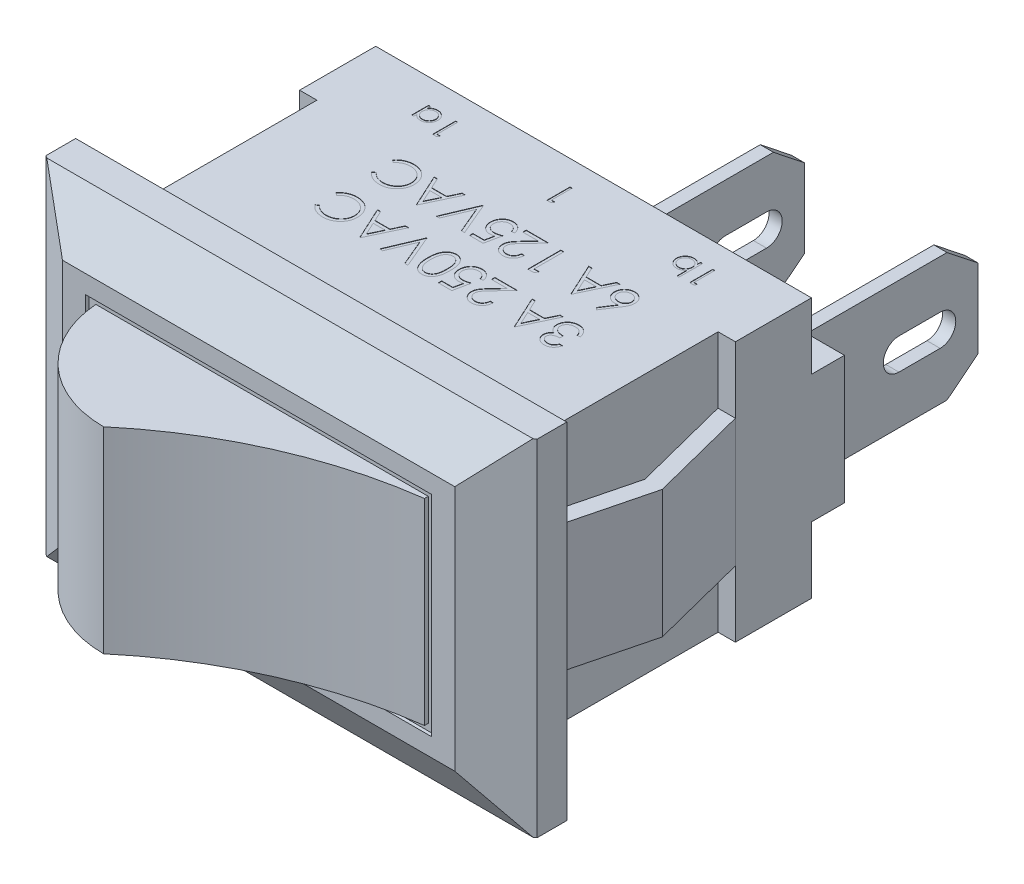
SolidWorks part; units mm, degrees
ref_plane "Front Plane" through (0, 0, 0) normal (0, 0, 1) x (1, 0, 0)
ref_plane "Top Plane" through (0, 0, 0) normal (0, 1, 0) x (1, 0, 0)
ref_plane "Right Plane" through (0, 0, 0) normal (1, 0, 0) x (0, 0, -1)
sketch "Sketch1" plane through (0, 0, 0) normal (0, 0, 1) x (1, 0, 0)
  line L1 (-7.455, 5.24) -> (7.455, 5.24)
  line L2 (-7.455, 5.24) -> (-7.455, -5.24)
  line L3 (-7.455, -5.24) -> (7.455, -5.24)
  line L4 (7.455, 5.24) -> (7.455, -5.24)
  dimension "D1" = 14.91
  dimension "D2" = 7.455
  dimension "D3" = 10.48
  dimension "D4" = 5.24
extrude "Boss-Extrude1" add sketch "Sketch1" against normal blind 1.9
sketch "Sketch2" plane through (0, -5.24, 0) normal (0, -1, 0) x (1, 0, 0)
  line L0 (-7.455, -1) -> (-5.955, 0)
  line L1 (-7.455, -1.9) -> (-7.455, 0) construction
  line L2 (-7.455, 0) -> (7.455, 0) construction
  line L3 (-5.955, 0) -> (-7.455, 0)
  line L4 (-7.455, 0) -> (-7.455, -1)
  line L5 (7.455, -1) -> (7.455, 0)
  line L6 (7.455, -1.9) -> (7.455, 0) construction
  line L7 (7.455, 0) -> (5.955, 0)
  line L8 (5.955, 0) -> (7.455, -1)
  dimension "D1" = 1.5
  dimension "D2" = 1.5
  dimension "D3" = 1
  dimension "D4" = 1
sketch "Sketch4" plane through (-7.455, 0, 0) normal (-1, 0, 0) x (0, 0, 1)
  line L0 (-0.95, -5.24) -> (0, -5.24)
  line L1 (-1.9, -5.24) -> (0, -5.24) construction
  line L2 (0, 5.24) -> (0, -5.24) construction
  line L3 (0, -5.24) -> (0, -3.74)
  line L4 (0, -3.74) -> (-0.95, -5.24)
  line L5 (-0.95, 5.24) -> (0, 3.74)
  line L6 (-1.9, 5.24) -> (0, 5.24) construction
  line L7 (0, 3.74) -> (0, 5.24)
  line L8 (0, 5.24) -> (-0.95, 5.24)
  dimension "D1" = 1.5
  dimension "D2" = 1.5
extrude "Cut-Extrude2" cut sketch "Sketch2" against normal through all
extrude "Cut-Extrude3" cut sketch "Sketch4" against normal through all
sketch "Sketch5" plane through (0, 0, 0) normal (0, 0, 1) x (1, 0, 0)
  line L1 (-5.25, 3.185) -> (5.25, 3.185)
  line L2 (-5.25, 3.185) -> (-5.25, -3.185)
  line L3 (-5.25, -3.185) -> (5.25, -3.185)
  line L4 (5.25, 3.185) -> (5.25, -3.185)
  line L5 (-5.05, 2.985) -> (5.05, 2.985)
  line L6 (-5.05, 2.985) -> (-5.05, -2.985)
  line L7 (-5.05, -2.985) -> (5.05, -2.985)
  line L8 (5.05, 2.985) -> (5.05, -2.985)
  dimension "D1" = 10.5
  dimension "D2" = 5.25
  dimension "D3" = 6.37
  dimension "D4" = 3.185
  dimension "D5" = 0.2
  dimension "D6" = 0.2
  dimension "D7" = 0.2
  dimension "D8" = 0.2
extrude "Cut-Extrude4" cut sketch "Sketch5" against normal blind 0.1
sketch "Sketch6" plane through (0, 0, -1.9) normal (0, 0, -1) x (-1, 0, 0)
  line L1 (-6.09, 3.95) -> (6.09, 3.95)
  line L2 (-6.09, 3.95) -> (-6.09, -3.95)
  line L3 (-6.09, -3.95) -> (6.09, -3.95)
  line L4 (6.09, 3.95) -> (6.09, -3.95)
  dimension "D1" = 12.18
  dimension "D2" = 6.09
  dimension "D3" = 7.9
  dimension "D4" = 3.95
extrude "Boss-Extrude2" add sketch "Sketch6" along normal blind 8.27
sketch "Sketch7" plane through (0, 3.95, 0) normal (0, 1, 0) x (1, 0, 0)
  line L1 (6.09, 10.17) -> (6.615, 10.17)
  line L2 (6.09, 10.17) -> (6.09, 7.86)
  line L3 (6.09, 7.86) -> (6.615, 7.86)
  line L4 (6.615, 10.17) -> (6.615, 7.86)
  line L5 (-6.09, 10.17) -> (-6.615, 10.17)
  line L6 (-6.09, 10.17) -> (-6.09, 7.86)
  line L7 (-6.09, 7.86) -> (-6.615, 7.86)
  line L8 (-6.615, 10.17) -> (-6.615, 7.86)
  point P10 (0, 0)
  dimension "D1" = 13.23
  dimension "D2" = 2.31
extrude "Boss-Extrude3" add sketch "Sketch7" against normal up to vertex (7.9 mm away) up to point (-6.09, -3.95, -10.17)
sketch "Sketch8" plane through (0, 0, 0) normal (0, 1, 0) x (1, 0, 0)
  line L0 (-6.615, 7.86) -> (-6.085, 7.86)
  line L1 (-6.085, 7.86) -> (-6.8453, 4.8806)
  line L2 (-6.8453, 4.8806) -> (-6.09, 1.9)
  line L3 (-6.09, 1.9) -> (-6.62, 1.9)
  line L4 (-6.62, 1.9) -> (-7.3753, 4.8806)
  line L5 (-7.3753, 4.8806) -> (-6.615, 7.86)
  point P2 (-6.6366, 7.8534)
  point P7 (-7.4396, 5.0917)
  point P8 (0, 0)
  point P9 (-6.0923, 1.9118)
  point P12 (-6.0654, 7.8569)
  point P13 (-6.0907, 7.7859)
  point P16 (-7.3753, 4.8806)
  point P17 (-7.3753, 4.8806)
  point P18 (-6.8453, 4.8806)
  point P19 (-7.3753, 4.8806)
  dimension "D1" = 0.53
  dimension "D2" = 0.53
  dimension "D3" = 0
  dimension "D4" = 0
  dimension "D5" = 0
  dimension "D6" = 151.465
extrude "Boss-Extrude4" add sketch "Sketch8" along normal blind 1.94 and the other way blind 1.94
mirror "Mirror1" about plane through (0, 0, 0) normal (1, 0, 0) of "Boss-Extrude4"
sketch "Sketch9" plane through (0, 0, -10.17) normal (0, 0, -1) x (-1, 0, 0)
  line L0 (-6.615, -1.94) -> (-6.615, 1.94) construction
  line L1 (-6.615, 1.94) -> (-5.465, 1.94)
  line L2 (-6.615, 1.94) -> (-6.615, -1.94)
  line L3 (-6.615, -1.94) -> (-5.465, -1.94)
  line L4 (-3.915, 1.94) -> (-3.915, -1.94)
  line L5 (6.615, -3.95) -> (6.615, 3.95) construction
  line L6 (-1.35, 1.94) -> (-0.2, 1.94)
  line L7 (-1.35, 1.94) -> (-1.35, -1.94)
  line L8 (-1.35, -1.94) -> (-0.2, -1.94)
  line L9 (1.35, 1.94) -> (1.35, -1.94)
  line L10 (6.615, 1.94) -> (5.465, 1.94)
  line L11 (6.615, 1.94) -> (6.615, -1.94)
  line L12 (6.615, -1.94) -> (5.465, -1.94)
  line L13 (3.915, 1.94) -> (3.915, -1.94)
  line L14 (-6.615, -3.95) -> (-6.615, 3.95) construction
  line L15 (-5.065, 1.94) -> (-3.915, 1.94)
  line L17 (-5.465, 1.94) -> (-5.465, -1.94)
  line L19 (-5.065, 1.94) -> (-5.065, -1.94)
  line L21 (-0.2, 1.94) -> (-0.2, -1.94)
  line L23 (0.2, 1.94) -> (0.2, -1.94)
  line L25 (5.065, 1.94) -> (5.065, -1.94)
  line L27 (5.465, 1.94) -> (5.465, -1.94)
  line L28 (0.2, 1.94) -> (1.35, 1.94)
  line L29 (5.065, 1.94) -> (3.915, 1.94)
  line L30 (5.065, -1.94) -> (3.915, -1.94)
  line L31 (0.2, -1.94) -> (1.35, -1.94)
  line L32 (-5.065, -1.94) -> (-3.915, -1.94)
  point P0 (0, 0)
  dimension "D1" = 2.7
  dimension "D2" = 1.35
  dimension "D3" = 0.4
  dimension "D4" = 1.15
  dimension "D5" = 1.15
  dimension "D6" = 0.4
  dimension "D7" = 0.4
  dimension "D8" = 1.15
  dimension "D9" = 2.565
  dimension "D10" = 1.15
extrude "Boss-Extrude5" add sketch "Sketch9" along normal blind 1
sketch "Sketch10" plane through (0, 0, 0) normal (1, 0, 0) x (0, 0, -1)
  line L0 (10.17, 1.94) -> (15.4293, 1.94)
  line L1 (15.4293, 1.94) -> (16.37, 1.195)
  line L2 (16.37, 1.195) -> (16.37, -1.195)
  line L3 (16.37, -1.195) -> (15.4293, -1.94)
  line L4 (15.4293, -1.94) -> (10.17, -1.94)
  line L5 (10.17, -1.94) -> (10.17, 1.94)
  line L6 (13.97, 0) -> (15.22, 0) construction
  line L7 (13.97, 0.475) -> (15.22, 0.475)
  line L8 (13.97, -0.475) -> (15.22, -0.475)
  arc A0 (13.97, 0.475) -> (13.97, -0.475) centre (13.97, 0) ccw
  arc A1 (15.22, -0.475) -> (15.22, 0.475) centre (15.22, 0) ccw
  point P2 (14.595, 0)
  point P13 (15.22, 0.3666)
  point P15 (14.887, 0.4844)
  dimension "D1" = 2.39
  dimension "D2" = 1.2
  dimension "D3" = 1.2
  dimension "D4" = 3.88
  dimension "D5" = 0.745
  dimension "D6" = 6.2
  dimension "D7" = 1.195
  dimension "D8" = 1.25
  dimension "D9" = 1.15
  dimension "D10" = 0.95
extrude "Boss-Extrude6" add sketch "Sketch10" along normal blind 0.2 and the other way blind 0.2
ref_plane "Plane1" through (2.635, 0, 0) normal (1, 0, 0) x (0, 0, -1)
mirror "Mirror2" about plane through (2.635, 0, 0) normal (1, 0, 0) of "Boss-Extrude6"
sketch "Sketch11" plane through (0, 3.95, 0) normal (0, 1, 0) x (1, 0, 0)
  line L0 (4.17, 5.9) -> (-3.28, 5.9) construction
  line L1 (4.17, 7.62) -> (-3.28, 7.62) construction
  line L2 (6.09, 7.86) -> (6.09, 1.9) construction
  line L3 (-6.09, 1.9) -> (6.09, 1.9) construction
  line L4 (4.67, 9.42) -> (3.27, 9.42) construction
  line L5 (0.77, 9.42) -> (-0.63, 9.42) construction
  line L6 (-3.13, 9.42) -> (-4.53, 9.42) construction
  line L7 (6.615, 7.86) -> (6.615, 10.17) construction
  text T0 "3A 250VAC" font "Century Gothic" height 1
  text T1 "6A 125VAC" font "Century Gothic" height 1
  text T2 "1b" font "Century Gothic" height 0.7
  text T3 "1" font "Century Gothic" height 0.7
  text T4 "1a" font "Century Gothic" height 0.7
  point P13 (4.17, 9.512)
  dimension "D1" = 1.92
  dimension "D2" = 7.45
  dimension "D3" = 1.72
  dimension "D4" = 4
  dimension "D5" = 1.4
  dimension "D6" = 1.4
  dimension "D7" = 1.4
  dimension "D8" = 2.5
  dimension "D9" = 2.5
  dimension "D10" = 1.8
  dimension "D11" = 1.945
extrude "Cut-Extrude5" cut sketch "Sketch11" against normal blind 0.01
sketch "Sketch12" plane through (0, -3.95, 0) normal (0, -1, 0) x (1, 0, 0)
  line L0 (-4.79, -3.2) -> (-1.29, -3.2) construction
  line L1 (-4.79, -5.7) -> (-0.79, -5.7) construction
  line L2 (-4.665, -9.25) -> (-3.265, -9.25) construction
  line L3 (-0.765, -9.25) -> (0.635, -9.25) construction
  line L4 (3.135, -9.25) -> (4.535, -9.25) construction
  line L5 (-6.615, -10.17) -> (-6.615, -7.86) construction
  line L6 (-7.455, -1.9) -> (7.455, -1.9) construction
  line L7 (-6.09, -7.86) -> (-6.09, -1.9) construction
  text T0 "KCD1" font "Century Gothic" height 1
  text T1 "CE" font "Century Gothic" height 1
  text T2 "2a" font "Century Gothic" height 0.7
  text T3 "2" font "Century Gothic" height 0.7
  text T4 "2b" font "Century Gothic" height 0.7
  dimension "D1" = 1.4
  dimension "D2" = 1.4
  dimension "D3" = 1.4
  dimension "D4" = 1.95
  dimension "D5" = 2.5
  dimension "D6" = 2.5
  dimension "D7" = 3.5
  dimension "D8" = 1.3
  dimension "D9" = 1.3
  dimension "D10" = 4
  dimension "D11" = 3.8
  dimension "D12" = 1.3
  dimension "D13" = 3.55
extrude "Cut-Extrude6" cut sketch "Sketch12" against normal blind 0.01
sketch "Sketch13" plane through (0, 0, 0) normal (0, 0, 1) x (1, 0, 0)
  line L0 (5.05, 2.985) -> (-5.05, 2.985) construction
  line L1 (5.05, -2.985) -> (5.05, 2.985) construction
  line L2 (-5.05, -2.985) -> (5.05, -2.985) construction
  line L3 (-5.05, 2.985) -> (-5.05, -2.985) construction
  line L4 (5.05, 2.985) -> (-5.05, 2.985)
  line L5 (5.05, -2.985) -> (5.05, 2.985)
  line L6 (-5.05, -2.985) -> (5.05, -2.985)
  line L7 (-5.05, 2.985) -> (-5.05, -2.985)
extrude "Boss-Extrude7" add sketch "Sketch13" along normal blind 3
sketch "Sketch16" plane through (0, 2.985, 0) normal (0, 1, 0) x (1, 0, 0)
  line L0 (-5.05, 0.1) -> (-5.05, -3) construction
  line L1 (5.05, -3) -> (-5.05, -3) construction
  line L2 (5.05, 0.1) -> (-5.05, 0.1) construction
  line L3 (5.05, 0.1) -> (5.05, -3) construction
  line L6 (-5.05, 0.1) -> (-5.05, -3)
  line L7 (5.05, -3) -> (-1.7071, -3)
  line L8 (5.05, -0.0148) -> (5.05, -3)
  arc A0 (5.05, -0.0148) -> (-1.7071, -3) centre (6.7863, -13.0852) ccw
  arc A1 (0.9855, -1.2446) -> (-1.8623, -3) centre (-1.8623, 0.1877) ccw
  point P3 (0, 0)
  point P4 (-2.4767, -0.2888)
  point P5 (-1.7596, 0)
  point P9 (0, 0)
  point P15 (0, 0)
  point P17 (0.9855, -1.2446)
extrude "Cut-Extrude9" cut sketch "Sketch16" against normal blind 8 contours L7 A0 L8
sketch "Sketch17" plane through (0, 2.985, 0) normal (0, 1, 0) x (1, 0, 0)
  line L0 (-5.05, 0.1) -> (-5.05, -3) construction
  line L1 (-1.7071, -3) -> (-5.05, -3) construction
  line L4 (-5.05, 0.1) -> (-5.05, -3)
  line L5 (-1.7071, -3) -> (-5.05, -3)
  line L8 (-5.0412, 0.1005) -> (-5.05, 0.1)
  arc A0 (-5.0412, 0.1005) -> (-1.7071, -3) centre (-1.7071, 0.3429) ccw
extrude "Cut-Extrude10" cut sketch "Sketch17" against normal blind 8
